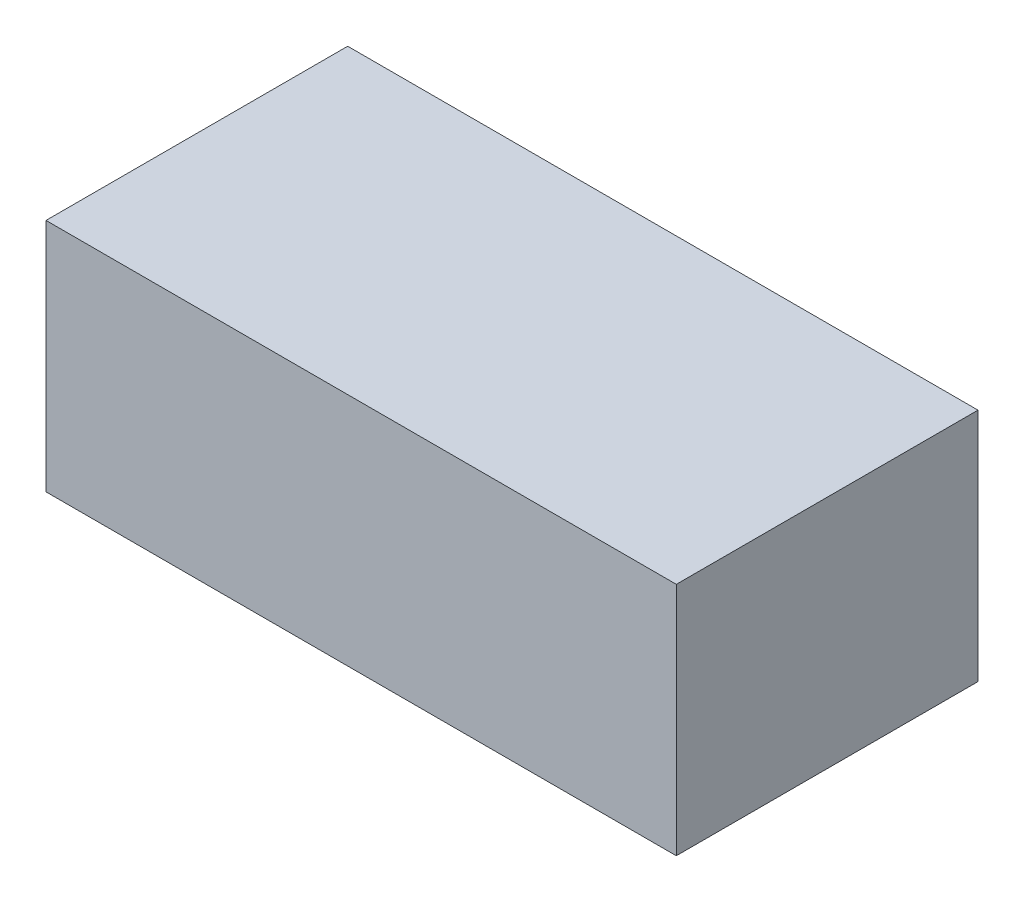
SolidWorks part; units mm, degrees
ref_plane "Front Plane" through (0, 0, 0) normal (0, 0, 1) x (1, 0, 0)
ref_plane "Top Plane" through (0, 0, 0) normal (0, 1, 0) x (1, 0, 0)
ref_plane "Right Plane" through (0, 0, 0) normal (1, 0, 0) x (0, 0, -1)
sketch "Sketch1" plane through (0, 0, 0) normal (0, 1, 0) x (1, 0, 0)
  line L1 (-37, 17.71) -> (37, 17.71)
  line L2 (-37, 17.71) -> (-37, -17.71)
  line L3 (-37, -17.71) -> (37, -17.71)
  line L4 (37, 17.71) -> (37, -17.71)
  line L5 (-37, 17.71) -> (37, -17.71) construction
  line L6 (-37, -17.71) -> (37, 17.71) construction
  point P0 (0, 0)
  dimension "D1" = 35.42
  dimension "D2" = 74
extrude "Boss-Extrude1" add sketch "Sketch1" along normal blind 27.6
